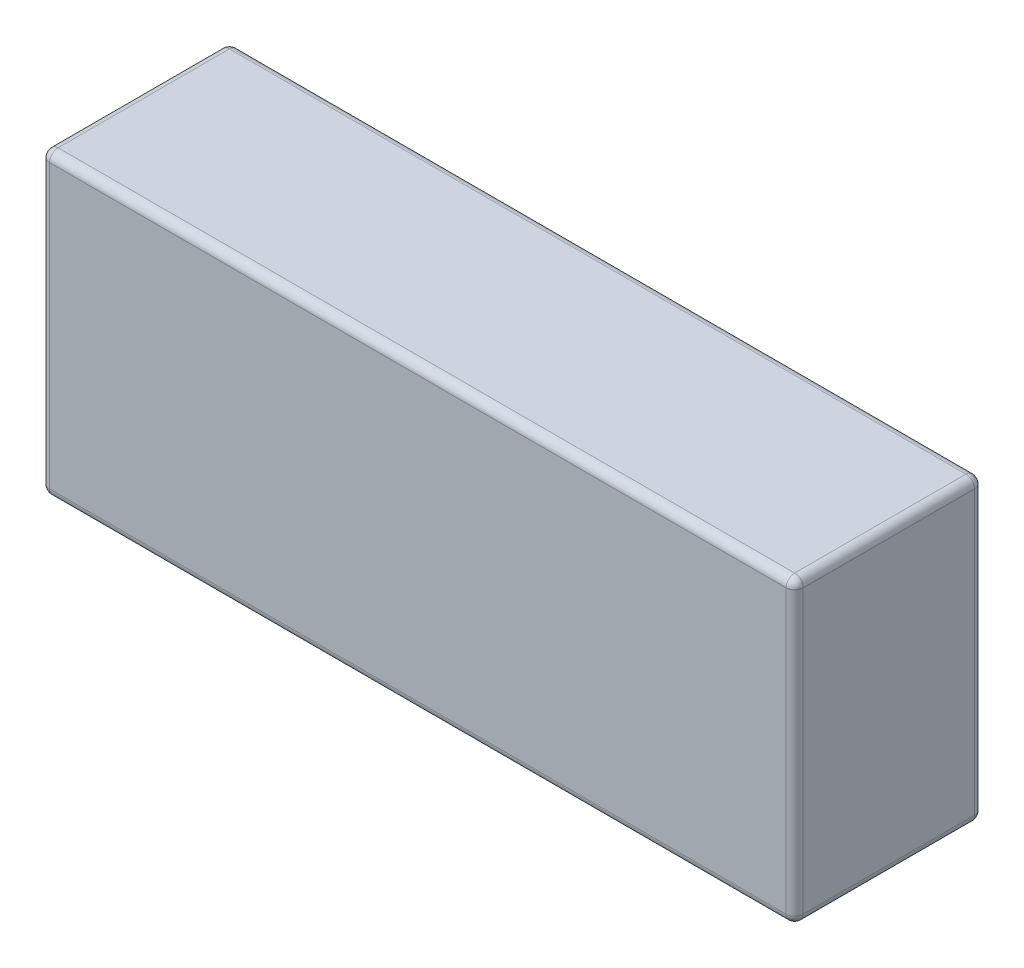
SolidWorks part; units mm, degrees
material "6061-T6 (SS)"
ref_plane "Front Plane" through (0, 0, 0) normal (0, 0, 1) x (1, 0, 0)
ref_plane "Top Plane" through (0, 0, 0) normal (0, 1, 0) x (1, 0, 0)
ref_plane "Right Plane" through (0, 0, 0) normal (1, 0, 0) x (0, 0, -1)
sketch "Sketch1" plane through (0, 0, 0) normal (0, 1, 0) x (1, 0, 0)
  line L1 (-44, -11) -> (44, -11)
  line L2 (-44, -11) -> (-44, 11)
  line L3 (-44, 11) -> (44, 11)
  line L4 (44, -11) -> (44, 11)
  line L5 (-44, -11) -> (44, 11) construction
  line L6 (-44, 11) -> (44, -11) construction
  point P0 (0, 0)
  dimension "D1" = 22
  dimension "D2" = 88
extrude "Boss-Extrude1" add sketch "Sketch1" along normal blind 35
fillet "Fillet1" radius 1 12 edges at (44, 17.5, -11) (-44, 17.5, -11) (-44, 17.5, 11) (44, 17.5, 11) (0, 35, 11) (-44, 35, 0) (0, 35, -11) (44, 35, 0) (0, 0, 11) (-44, 0, 0) (0, 0, -11) (44, 0, 0)
